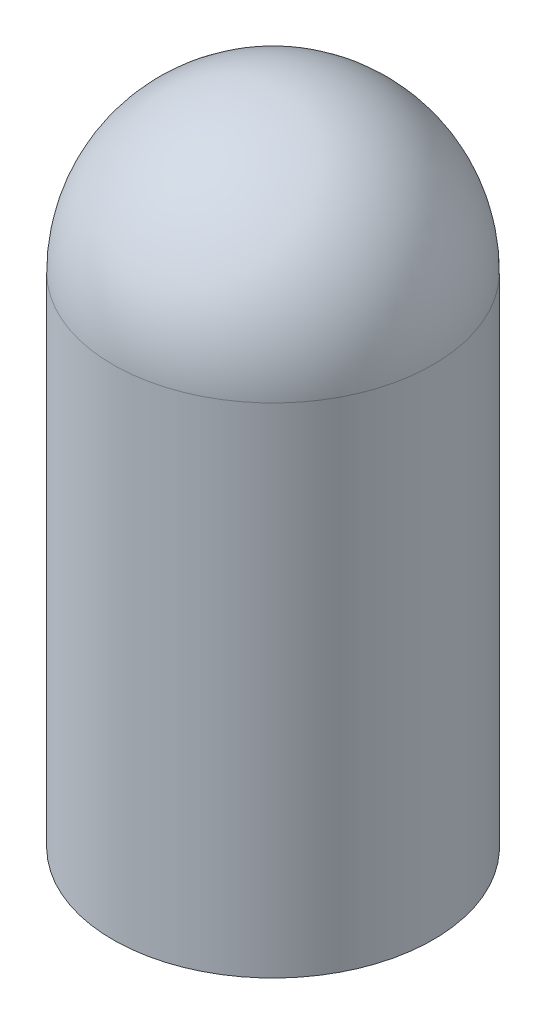
SolidWorks part; units mm, degrees
ref_plane "Front Plane" through (0, 0, 0) normal (0, 0, 1) x (1, 0, 0)
ref_plane "Top Plane" through (0, 0, 0) normal (0, 1, 0) x (1, 0, 0)
ref_plane "Right Plane" through (0, 0, 0) normal (1, 0, 0) x (0, 0, -1)
sketch "Sketch4" plane through (0, 0, 0) normal (0, 0, 1) x (1, 0, 0)
  line L0 (-2.5, 0) -> (-2.5, -7.7778)
  line L1 (-2.5, -7.7778) -> (2.5, -7.7778)
  line L2 (2.5, -7.7778) -> (2.5, 0)
  line L3 (0, 2.5) -> (0, -7.7778)
  arc A0 (-2.5, 0) -> (2.5, 0) centre (0, 0) cw
  dimension "D1" = 2.5
revolve "Revolve4" add sketch "Sketch4" angle 360 about L3
